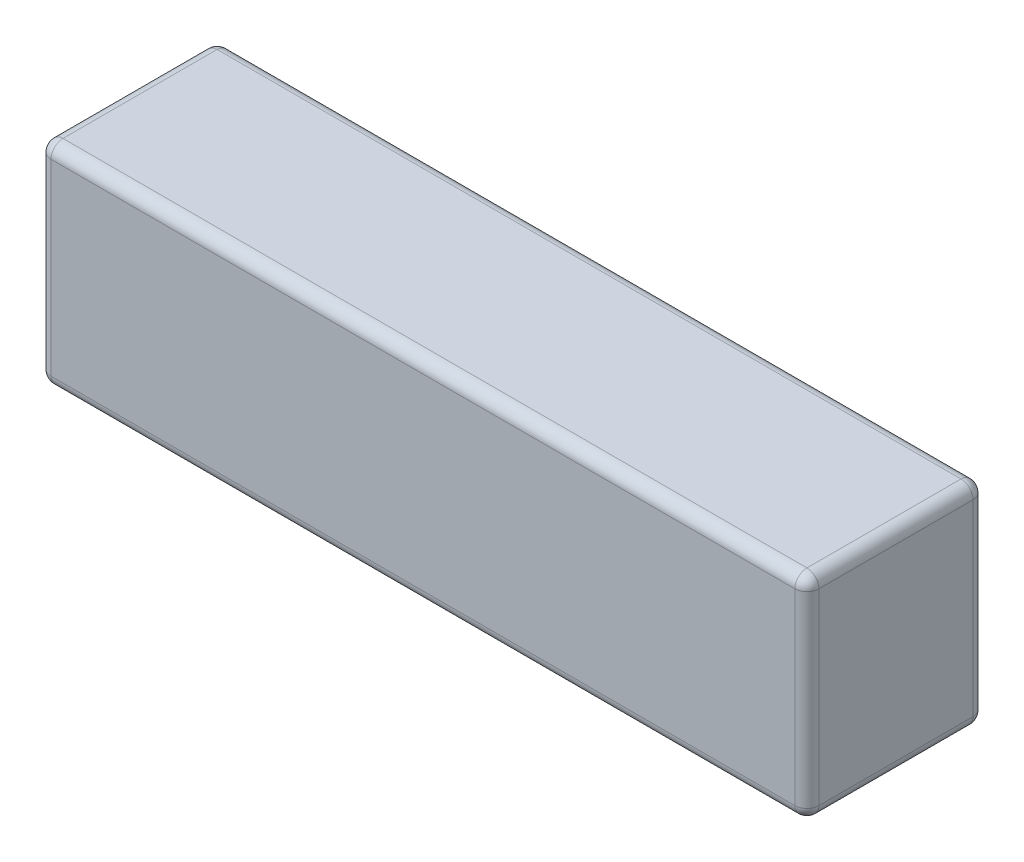
SolidWorks part; units mm, degrees
material "Silicon"
ref_plane "Front Plane" through (0, 0, 0) normal (0, 0, 1) x (1, 0, 0)
ref_plane "Top Plane" through (0, 0, 0) normal (0, 1, 0) x (1, 0, 0)
ref_plane "Right Plane" through (0, 0, 0) normal (1, 0, 0) x (0, 0, -1)
sketch "Sketch1" plane through (0, 0, 0) normal (0, 0, 1) x (1, 0, 0)
  line L1 (-159.5, -44) -> (159.5, -44)
  line L2 (-159.5, -44) -> (-159.5, 44)
  line L3 (-159.5, 44) -> (159.5, 44)
  line L4 (159.5, -44) -> (159.5, 44)
  line L5 (-159.5, -44) -> (159.5, 44) construction
  line L6 (-159.5, 44) -> (159.5, -44) construction
  point P0 (0, 0)
  dimension "D1" = 319
  dimension "D2" = 88
extrude "Boss-Extrude1" add sketch "Sketch1" along normal blind 74 contours L3 L4 L1 L2
fillet "Fillet1" radius 5 12 edges at (0, -44, 0) (159.5, 0, 0) (0, 44, 0) (-159.5, 44, 37) (-159.5, 0, 74) (-159.5, -44, 37) (-159.5, 0, 0) (0, -44, 74) (159.5, -44, 37) (159.5, 0, 74) (159.5, 44, 37) (0, 44, 74)
